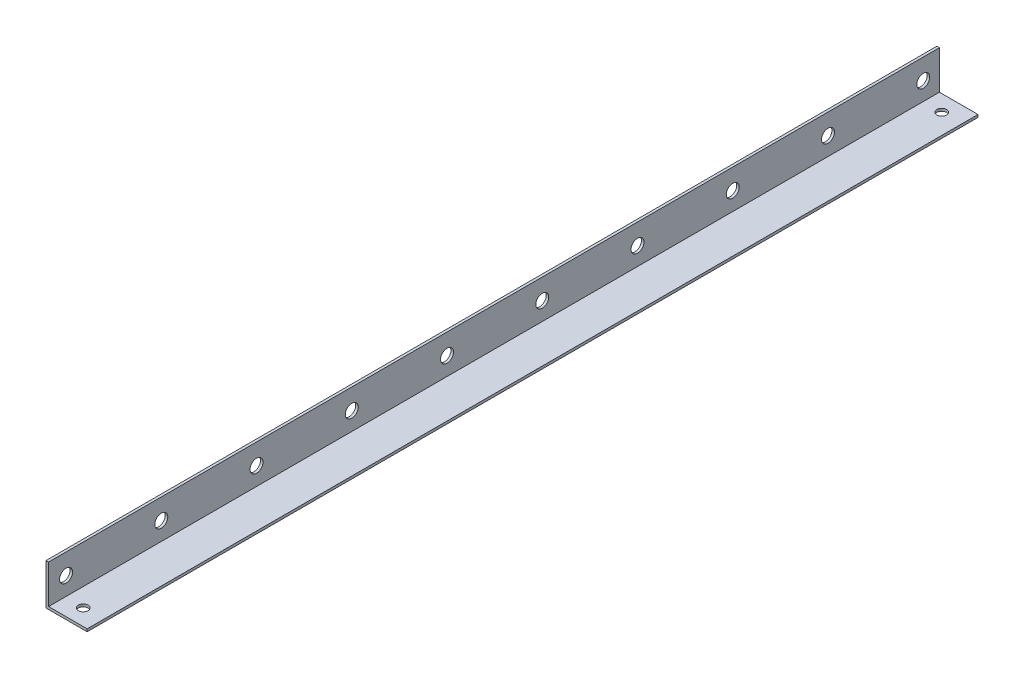
SolidWorks part; units mm, degrees
ref_plane "Front Plane" through (0, 0, 0) normal (0, 0, 1) x (1, 0, 0)
ref_plane "Top Plane" through (0, 0, 0) normal (0, 1, 0) x (1, 0, 0)
ref_plane "Right Plane" through (0, 0, 0) normal (1, 0, 0) x (0, 0, -1)
sketch "Sketch1" plane through (0, 0, 0) normal (0, 0, 1) x (1, 0, 0)
  line L0 (0, 0) -> (0, 25.4)
  line L3 (0, 25.4) -> (1.5875, 25.4)
  line L4 (1.5875, 1.5875) -> (1.5875, 25.4)
  line L5 (1.5875, 1.5875) -> (25.4, 1.5875)
  line L7 (0, 0) -> (25.4, 0)
  line L8 (25.4, 1.5875) -> (25.4, 0)
  dimension "D1" = 1.5875
  dimension "D2" = 25.4
  dimension "D3" = 25.4
extrude "Boss-Extrude1" add sketch "Sketch1" along normal mid plane 550
sketch "Sketch2" plane through (1.5875, 0, 0) normal (1, 0, 0) x (0, 0, -1)
  line L0 (-275, 12.7) -> (275, 12.7) construction
  line L5 (-275, 1.5875) -> (-275, 25.4) construction
  line L6 (275, 1.5875) -> (275, 25.4) construction
  line L7 (-275, 25.4) -> (275, 25.4) construction
  circle A0 centre (265, 12.7) radius 4
  circle A3 centre (-275, 12.7) radius 12.7 construction
  circle A4 centre (206.2, 12.7) radius 4
  circle A5 centre (147.4, 12.7) radius 4
  circle A6 centre (88.6, 12.7) radius 4
  circle A7 centre (29.8, 12.7) radius 4
  circle A8 centre (-29, 12.7) radius 4
  circle A9 centre (-87.8, 12.7) radius 4
  circle A10 centre (-146.6, 12.7) radius 4
  circle A11 centre (-205.4, 12.7) radius 4
  circle A12 centre (-264.2, 12.7) radius 4
  dimension "D1" = 25.4
  dimension "D2" = 8
  dimension "D3" = 10
  dimension "D5" = 58.8
  dimension "D4" = 10
extrude "Cut-Extrude1" cut sketch "Sketch2" against normal through all
sketch "Sketch3" plane through (0, 1.5875, 0) normal (0, 1, 0) x (1, 0, 0)
  line L0 (13, 275) -> (13, 265) construction
  line L1 (25.4, 275) -> (1.5875, 275) construction
  line L2 (0, -275) -> (0, 275) construction
  circle A0 centre (13, 265) radius 3
  dimension "D1" = 6
  dimension "D2" = 13
  dimension "D3" = 10
extrude "Cut-Extrude2" cut sketch "Sketch3" along normal through all and the other way through all
mirror "Mirror1" about plane through (0, 0, 0) normal (0, 0, 1) of "Cut-Extrude2"
